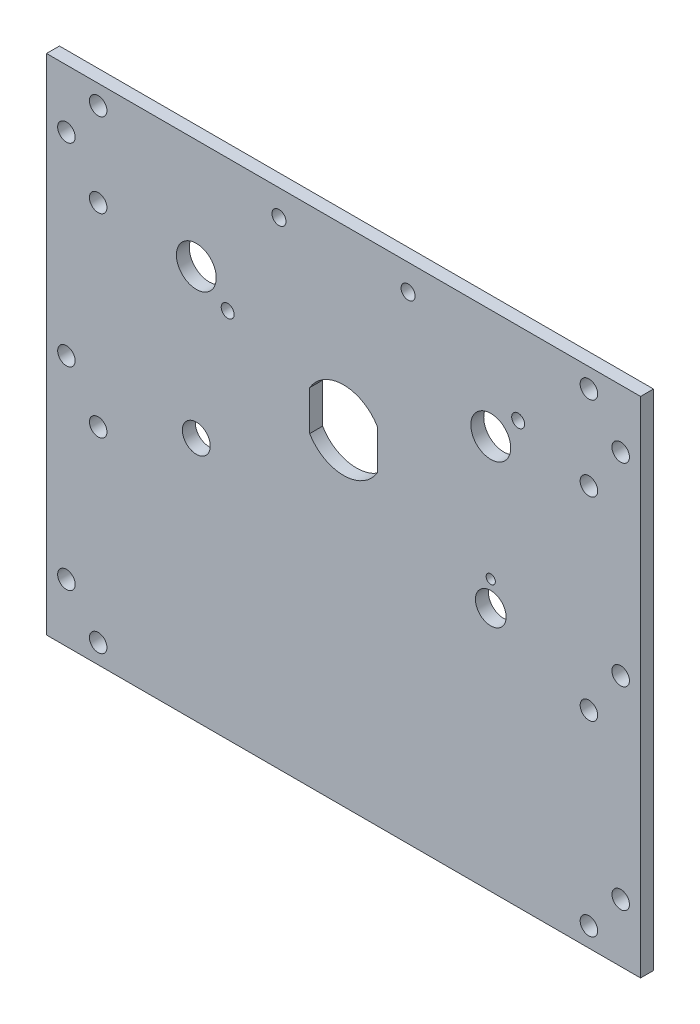
SolidWorks part; units mm, degrees
ref_plane "Front Plane" through (0, 0, 0) normal (0, 0, 1) x (1, 0, 0)
ref_plane "Top Plane" through (0, 0, 0) normal (0, 1, 0) x (1, 0, 0)
ref_plane "Right Plane" through (0, 0, 0) normal (1, 0, 0) x (0, 0, -1)
sketch "Sketch1" plane through (0, 0, 0) normal (0, 0, 1) x (1, 0, 0)
  line L8 (0, 123.825) -> (-146.05, 123.825)
  line L9 (-146.05, 123.825) -> (-146.05, 0)
  line L10 (-146.05, 0) -> (0, 0)
  line L11 (0, 0) -> (0, 123.825)
extrude "Boss-Extrude1" add sketch "Sketch1" against normal blind 3.175
hole_wizard "#6 Clearance Hole1" positions "Sketch3" profile "Sketch2" hole size "#6" standard "ANSI Inch" end condition through all
sketch "Sketch3" plane through (0, 0, -3.175) normal (0, 0, -1) x (-1, 0, 0)
  line L0 (88.9, 117.475) -> (57.15, 117.475) construction
  point P0 (12.7, 119.0625)
  point P9 (133.35, 119.0625)
  point P12 (141.1605, 109.5375)
  point P15 (133.35, 98.425)
  point P18 (141.1605, 61.9125)
  point P21 (133.35, 50.673)
  point P24 (133.35, 4.7625)
  point P27 (12.7, 4.7625)
  point P30 (12.7, 50.673)
  point P33 (12.7, 98.425)
  point P36 (4.8895, 109.5375)
  point P39 (141.1605, 14.2875)
  point P42 (4.8895, 14.2875)
  point P45 (4.8895, 61.9125)
sketch "Sketch2" plane through (-12.7, 119.0625, -3.175) normal (1, 0, 0) x (0, 1, 0)
  line L0 (0, 0) -> (0, 3.175)
  line L1 (0, 3.175) -> (2.1526, 3.175)
  line L2 (2.1526, 3.175) -> (2.1526, 0)
  line L5 (2.1526, 0) -> (0, 0)
  line L11 (0, -6.35) -> (0, 107.95) construction
  dimension "Thru Hole Dia." = 4.3053
  dimension "Thru Hole Depth" = 3.175
sketch "Sketch4" plane through (0, 0, -3.175) normal (0, 0, -1) x (-1, 0, 0)
  line L0 (109.22, 96.901) -> (89.8757, 96.901) construction
  line L1 (109.22, 96.901) -> (101.5141, 91.3023) construction
  line L2 (81.3435, 85.0323) -> (81.3435, 75.2417)
  line L3 (64.7065, 75.2417) -> (64.7065, 85.0323)
  line L5 (36.83, 96.901) -> (21.0814, 96.901) construction
  line L6 (36.83, 96.901) -> (30.0948, 103.6362) construction
  circle A0 centre (36.83, 96.901) radius 4.9022
  circle A1 centre (36.83, 60.325) radius 3.7703
  circle A2 centre (109.22, 60.325) radius 3.429
  circle A3 centre (109.22, 96.901) radius 4.9022
  circle A4 centre (36.83, 66.525) radius 1.125
  circle A5 centre (101.5141, 91.3023) radius 1.5875
  arc A6 (81.3435, 85.0323) -> (64.7065, 85.0323) centre (73.025, 80.137) ccw
  arc A7 (64.7065, 75.2417) -> (81.3435, 75.2417) centre (73.025, 80.137) ccw
  circle A8 centre (30.0948, 103.6362) radius 1.5875
  dimension "D1" = 7.5406
  dimension "D2" = 9.8044
  dimension "D3" = 6.858
  dimension "D4" = 2.25
  dimension "D5" = 3.175
  dimension "D7" = 9.8044
  dimension "D9" = 315
  dimension "D11" = 3.175
  dimension "D6" = 9.525
  dimension "D8" = 36
  dimension "D10" = 9.525
  dimension "D12" = 6.2
extrude "Switch Mount Holes" cut sketch "Sketch4" against normal through all
hole_wizard "#4 Clearance Hole1" positions "Sketch6" profile "Sketch5" hole size "#4" standard "ANSI Inch" end condition through all
sketch "Sketch6" plane through (0, 0, 0) normal (0, 0, 1) x (1, 0, 0)
  point P3 (-88.9, 117.475)
  point P6 (-57.15, 117.475)
sketch "Sketch5" plane through (-88.9, 117.475, 0) normal (1, 0, 0) x (0, -1, 0)
  line L0 (0, 0) -> (0, 3.175)
  line L1 (0, 3.175) -> (1.7272, 3.175)
  line L2 (1.7272, 3.175) -> (1.7272, 0)
  line L5 (1.7272, 0) -> (0, 0)
  line L11 (0, -6.35) -> (0, 107.95) construction
  dimension "Thru Hole Dia." = 3.4544
  dimension "Thru Hole Depth" = 3.175
